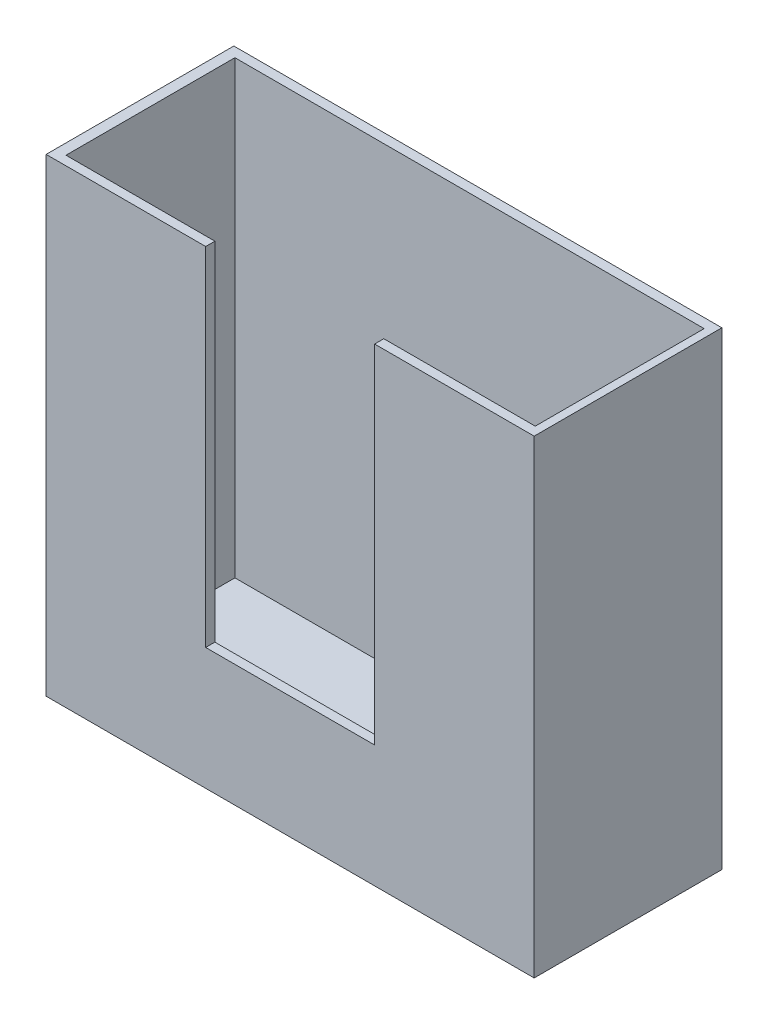
SolidWorks part; units mm, degrees
ref_plane "Front Plane" through (0, 0, 0) normal (0, 0, 1) x (1, 0, 0)
ref_plane "Top Plane" through (0, 0, 0) normal (0, 1, 0) x (1, 0, 0)
ref_plane "Right Plane" through (0, 0, 0) normal (1, 0, 0) x (0, 0, -1)
sketch "Sketch1" plane through (0, 0, 0) normal (0, 0, 1) x (1, 0, 0)
  line L1 (13, -12.5) -> (-13, -12.5)
  line L2 (13, -12.5) -> (13, 12.5)
  line L3 (13, 12.5) -> (-13, 12.5)
  line L4 (-13, -12.5) -> (-13, 12.5)
  line L5 (13, -12.5) -> (-13, 12.5) construction
  line L6 (13, 12.5) -> (-13, -12.5) construction
  point P0 (0, 0)
  point P6 (13, 0)
  point P7 (-13, 0)
  dimension "D1" = 25
  dimension "D2" = 26
extrude "Boss-Extrude1" add sketch "Sketch1" along normal blind 10 contours L2 L1 L4 L3
sketch "Sketch2" plane through (0, 12.5, 0) normal (0, 1, 0) x (1, 0, 0)
  line L1 (-12.4322, -0.5105) -> (12.5678, -0.5105)
  line L2 (-12.4322, -0.5105) -> (-12.4322, -9.5105)
  line L3 (-12.4322, -9.5105) -> (12.5678, -9.5105)
  line L4 (12.5678, -0.5105) -> (12.5678, -9.5105)
  line L5 (-12.4322, -0.5105) -> (12.5678, -9.5105) construction
  line L6 (-12.4322, -9.5105) -> (12.5678, -0.5105) construction
  point P0 (0.0678, -5.0105)
  dimension "D1" = 9
  dimension "D2" = 25
extrude "Cut-Extrude1" cut sketch "Sketch2" against normal blind 24 contours L2 L1 L4 L3
sketch "Sketch3" plane through (0, 0, 10) normal (0, 0, 1) x (1, 0, 0)
  line L5 (13, 12.5) -> (-13, 12.5) construction
  line L6 (-4.5, 12.5) -> (4.5, 12.5)
  line L7 (-4.5, 12.5) -> (-4.5, -6)
  line L8 (-4.5, -6) -> (4.5, -6)
  line L9 (4.5, 12.5) -> (4.5, -6)
  line L10 (-4.5, 12.5) -> (4.5, -6) construction
  line L11 (-4.5, -6) -> (4.5, 12.5) construction
  line L14 (-13, -12.5) -> (-13, 12.5) construction
  point P0 (0, 3.25)
  dimension "D1" = 18.5
  dimension "D2" = 9
  dimension "D3" = 8.5
extrude "Cut-Extrude2" cut sketch "Sketch3" against normal blind 5 contours L7 L6 L9 L8
